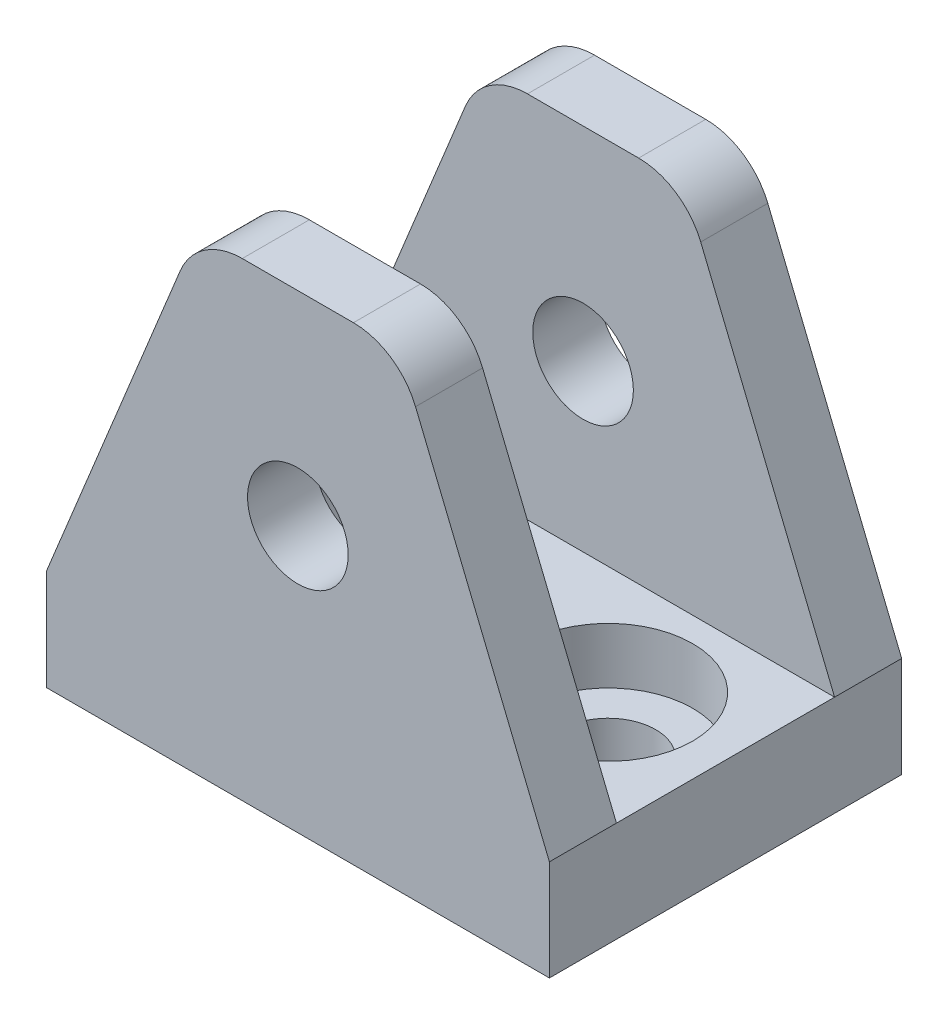
SolidWorks part; units mm, degrees
material "6061-T6 (SS)"
ref_plane "X-Y Datum" through (0, 0, 0) normal (0, 0, 1) x (1, 0, 0)
ref_plane "X-Z Datum" through (0, 0, 0) normal (0, 1, 0) x (1, 0, 0)
ref_plane "Y-Z Datum" through (0, 0, 0) normal (1, 0, 0) x (0, 0, -1)
sketch "Sketch1" plane through (0, 0, 0) normal (0, 1, 0) x (1, 0, 0)
  line L1 (-23.8125, -16.6751) -> (23.8125, -16.6751)
  line L2 (-23.8125, -16.6751) -> (-23.8125, 16.6751)
  line L3 (-23.8125, 16.6751) -> (23.8125, 16.6751)
  line L4 (23.8125, -16.6751) -> (23.8125, 16.6751)
  line L5 (-23.8125, -16.6751) -> (23.8125, 16.6751) construction
  line L6 (-23.8125, 16.6751) -> (23.8125, -16.6751) construction
  point P0 (0, 0)
  dimension "D1" = 47.625
  dimension "D2" = 33.3502
extrude "Boss-Extrude1" add sketch "Sketch1" along normal blind 44.45
sketch "Sketch2" plane through (0, 44.45, 0) normal (0, 1, 0) x (1, 0, 0)
  line L0 (23.8125, -16.6751) -> (23.8125, 16.6751) construction
  line L1 (-23.8125, -10.3251) -> (23.8125, -10.3251)
  line L2 (-23.8125, -10.3251) -> (-23.8125, 10.3251)
  line L3 (-23.8125, 10.3251) -> (23.8125, 10.3251)
  line L4 (23.8125, -10.3251) -> (23.8125, 10.3251)
  line L5 (-23.8125, -10.3251) -> (23.8125, 10.3251) construction
  line L6 (-23.8125, 10.3251) -> (23.8125, -10.3251) construction
  line L7 (23.8125, 16.6751) -> (-23.8125, 16.6751) construction
  point P0 (0, 0)
  dimension "D1" = 6.35
extrude "Cut-Extrude1" cut sketch "Sketch2" against normal offset from surface (34.925 mm away) 9.525 up to face at (0, 0, 0)
sketch "Sketch3" plane through (0, 0, -16.6751) normal (0, 0, -1) x (-1, 0, 0)
  line L9 (9.525, 44.45) -> (23.8125, 44.45)
  line L10 (-23.8125, 44.45) -> (23.8125, 44.45) construction
  line L11 (23.8125, 44.45) -> (23.8125, 9.525)
  line L12 (23.8125, 44.45) -> (23.8125, 0) construction
  line L13 (23.8125, 9.525) -> (9.525, 44.45)
  line L14 (-23.8125, 0) -> (23.8125, 0) construction
  line L15 (0, 0) -> (0, -50000) construction
  line L17 (-23.8125, 44.45) -> (-23.8125, 9.525)
  line L18 (-9.525, 44.45) -> (-23.8125, 44.45)
  line L19 (-23.8125, 9.525) -> (-9.525, 44.45)
  line M2 (23.8125, 0) -> (23.8125, 44.45)
  line M3 (23.8125, 44.45) -> (-23.8125, 44.45)
  line M4 (-23.8125, 44.45) -> (-23.8125, 0)
  dimension "D1" = 9.525
  dimension "D2" = 19.05
extrude "Cut-Extrude2" cut sketch "Sketch3" against normal through all and the other way through all contours L13 M2 M3 | L19 M4 M3
hole_wizard "CBORE for M8 Hex Head Bolt1" positions "Sketch6" profile "Sketch7" counterbore size "M8" standard "ANSI Metric"
sketch "Sketch6" plane through (0, 9.525, 0) normal (0, 1, 0) x (1, 0, 0)
  line L0 (0, 0) -> (0, 50000) construction
  line L1 (0, 0) -> (50000, 0) construction
  point P0 (-12.7, 0)
  point P2 (12.7, 0)
  dimension "D1" = 12.7
  dimension "D2" = 12.7
sketch "Sketch7" plane through (-12.7, 9.525, 0) normal (1, 0, 0) x (0, 0, 1)
  line L0 (0, 0) -> (0, 16.002)
  line L1 (0, 16.002) -> (4.5, 13.2981)
  line L2 (4.5, 13.2981) -> (4.5, 5.3)
  line L3 (4.5, 5.3) -> (8, 5.3)
  line L4 (8, 5.3) -> (8, 0)
  line L5 (8, 0) -> (0, 0)
  line L10 (0, 16.002) -> (-4.5, 13.2981) construction
  line L11 (0, -6.35) -> (0, 107.95) construction
  dimension "Hole Dia." = 9
  dimension "Hole Depth" = 16.002
  dimension "C'Bore Dia." = 16
  dimension "C'Bore Depth" = 5.3
  dimension "Drill Angle" = 118
sketch "Sketch8" plane through (0, 9.525, 0) normal (0, 1, 0) x (1, 0, 0)
  line L0 (-3.175, 0) -> (3.175, 0) construction
  line L1 (-3.175, 6.35) -> (3.175, 6.35)
  line L2 (-3.175, -6.35) -> (3.175, -6.35)
  arc A0 (-3.175, 6.35) -> (-3.175, -6.35) centre (-3.175, 0) ccw
  arc A1 (3.175, -6.35) -> (3.175, 6.35) centre (3.175, 0) ccw
  point P3 (0, 0)
  dimension "D2" = 6.35
  dimension "D1" = 6.35
fillet "Fillet3" radius 6.35 4 edges at (9.525, 44.45, 13.5001) (-9.525, 44.45, 13.5001) (9.525, 44.45, -13.5001) (-9.525, 44.45, -13.5001)
extrude "Cut-Extrude3" [suppressed] cut sketch "Sketch8" against normal through all
hole_wizard "3/8 (0.375) Diameter Hole1" positions "Sketch9" profile "Sketch11" hole size "3/8" standard "ANSI Inch" end condition through all
sketch "Sketch9" plane through (0, 0, 16.6751) normal (0, 0, 1) x (1, 0, 0)
  point P0 (0, 25.1617)
  point P9 (0, 0)
sketch "Sketch11" plane through (0, 25.1617, 16.6751) normal (1, 0, 0) x (0, -1, 0)
  line L0 (0, 0) -> (0, 33.3503)
  line L1 (0, 33.3503) -> (4.7625, 33.3503)
  line L2 (4.7625, 33.3503) -> (4.7625, 0)
  line L5 (4.7625, 0) -> (0, 0)
  line L11 (0, -6.35) -> (0, 107.95) construction
  dimension "Thru Hole Dia." = 9.525
  dimension "Thru Hole Depth" = 33.3503
